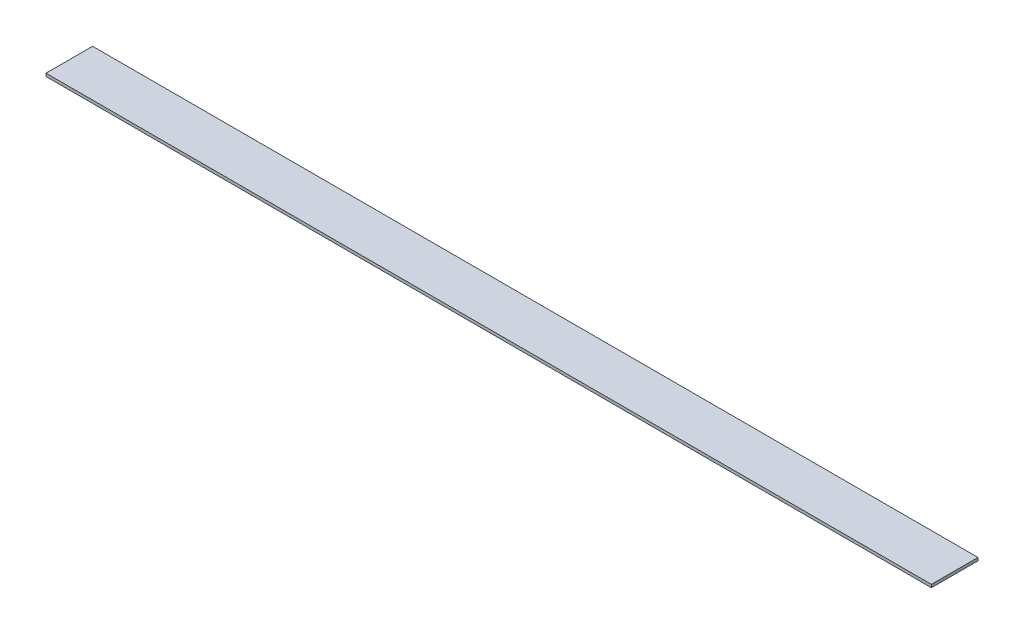
SolidWorks part; units mm, degrees
ref_plane "Front Plane" through (0, 0, 0) normal (0, 0, 1) x (1, 0, 0)
ref_plane "Top Plane" through (0, 0, 0) normal (0, 1, 0) x (1, 0, 0)
ref_plane "Right Plane" through (0, 0, 0) normal (1, 0, 0) x (0, 0, -1)
sketch "Sketch1" plane through (0, 0, 0) normal (0, 1, 0) x (1, 0, 0)
  line L1 (0, 0) -> (482.6, 0)
  line L2 (0, 0) -> (0, 25.4)
  line L3 (0, 25.4) -> (482.6, 25.4)
  line L4 (482.6, 0) -> (482.6, 25.4)
  dimension "D1" = 25.4
  dimension "D2" = 482.6
extrude "Boss-Extrude1" add sketch "Sketch1" along normal blind 1.5875
